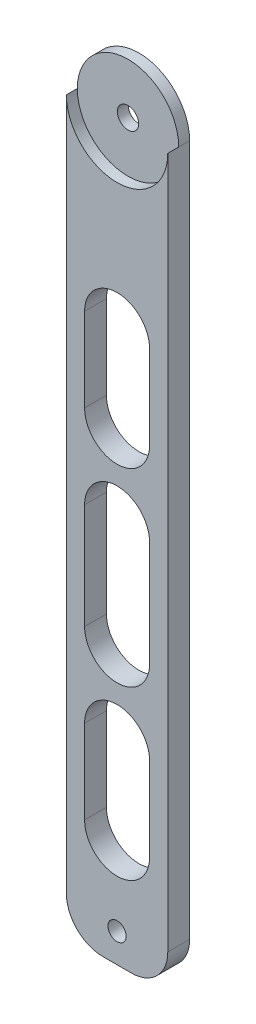
SolidWorks part; units mm, degrees
ref_plane "Plan de face" through (0, 0, 0) normal (0, 0, 1) x (1, 0, 0)
ref_plane "Plan de dessus" through (0, 0, 0) normal (0, 1, 0) x (1, 0, 0)
ref_plane "Plan de droite" through (0, 0, 0) normal (1, 0, 0) x (0, 0, -1)
sketch "Esquisse1" plane through (0, 0, 0) normal (0, 0, 1) x (1, 0, 0)
  line L1 (-12.0899, 21.2113) -> (15.7601, 21.2113)
  line L2 (-12.0899, 21.2113) -> (-12.0899, -178.7887)
  line L3 (-12.0899, -178.7887) -> (15.7601, -178.7887)
  line L4 (15.7601, 21.2113) -> (15.7601, -178.7887)
  arc A1 (15.7601, 21.2113) -> (-12.0899, 21.2113) centre (1.8351, 21.2113) ccw
  dimension "D1" = 27.85
  dimension "D2" = 200
extrude "Boss.-Extru.2" add sketch "Esquisse1" along normal blind 6 contours L4 L1 L2 L3 | L1 A1
sketch "Esquisse3" plane through (0, 0, 6) normal (0, 0, 1) x (1, 0, 0)
  line L0 (15.7601, 21.2113) -> (15.7601, -178.7887) construction
  line L1 (-12.0899, -178.7887) -> (15.7601, -178.7887) construction
  circle A0 centre (1.8351, -170.7887) radius 2.5
  dimension "D1" = 5
  dimension "D2" = 13.925
  dimension "D3" = 8
extrude "Enlèv. mat.-Extru.1" cut sketch "Esquisse3" against normal blind 6
sketch "Esquisse4" plane through (0, 0, 6) normal (0, 0, 1) x (1, 0, 0)
  circle A0 centre (1.8351, 21.2113) radius 13.925
extrude "Enlèv. mat.-Extru.2" cut sketch "Esquisse4" against normal blind 3
sketch "Esquisse5" plane through (0, 0, 3) normal (0, 0, 1) x (1, 0, 0)
  circle A0 centre (1.8351, 21.2113) radius 2.925
  dimension "D1" = 5.85
extrude "Enlèv. mat.-Extru.3" cut sketch "Esquisse5" against normal blind 3
sketch "Esquisse6" plane through (0, 0, 6) normal (0, 0, 1) x (1, 0, 0)
  line L0 (15.7601, 21.2113) -> (15.7601, -178.7887) construction
  line L1 (-7.0899, -27.7887) -> (10.7601, -27.7887)
  line L2 (-7.0899, -27.7887) -> (-7.0899, -50.7887)
  line L3 (-7.0899, -50.7887) -> (10.7601, -50.7887)
  line L4 (10.7601, -27.7887) -> (10.7601, -50.7887)
  line L5 (-7.0899, -73.7887) -> (10.7601, -73.7887)
  line L6 (-7.0899, -73.7887) -> (-7.0899, -102.7887)
  line L7 (-7.0899, -102.7887) -> (10.7601, -102.7887)
  line L8 (10.7601, -73.7887) -> (10.7601, -102.7887)
  line L9 (-7.0899, -125.7887) -> (10.7601, -125.7887)
  line L10 (-7.0899, -125.7887) -> (-7.0899, -148.7887)
  line L11 (-7.0899, -148.7887) -> (10.7601, -148.7887)
  line L12 (10.7601, -125.7887) -> (10.7601, -148.7887)
  line L13 (-12.0899, 21.2113) -> (-12.0899, -178.7887) construction
  line L14 (-12.0899, -178.7887) -> (15.7601, -178.7887) construction
  arc A0 (10.7601, -27.7887) -> (-7.0899, -27.7887) centre (1.8351, -27.7887) ccw
  arc A1 (-7.0899, -50.7887) -> (10.7601, -50.7887) centre (1.8351, -50.7887) ccw
  arc A2 (-7.0899, -73.7887) -> (10.7601, -73.7887) centre (1.8351, -73.7887) cw
  arc A3 (-7.0899, -102.7887) -> (10.7601, -102.7887) centre (1.8351, -102.7887) ccw
  arc A4 (10.7601, -125.7887) -> (-7.0899, -125.7887) centre (1.8351, -125.7887) ccw
  arc A5 (-7.0899, -148.7887) -> (10.7601, -148.7887) centre (1.8351, -148.7887) ccw
  dimension "D1" = 5
  dimension "D2" = 5
  dimension "D3" = 5
  dimension "D4" = 5
  dimension "D5" = 5
  dimension "D6" = 5
  dimension "D7" = 23
  dimension "D8" = 23
  dimension "D9" = 23
  dimension "D10" = 23
  dimension "D11" = 29
  dimension "D12" = 30
extrude "Enlèv. mat.-Extru.4" cut sketch "Esquisse6" against normal blind 10 contours L1 A0 | L4 L1 L2 L3 | L3 A1 | A2 L5 | L8 L5 L6 L7 | L7 A3 | L9 A4 | L12 L9 L10 L11 | L11 A5
fillet "Congé1" radius 10 1 edges at (-12.0899, -178.7887, 3)
fillet "Congé2" radius 10 1 edges at (15.7601, -178.7887, 3)
